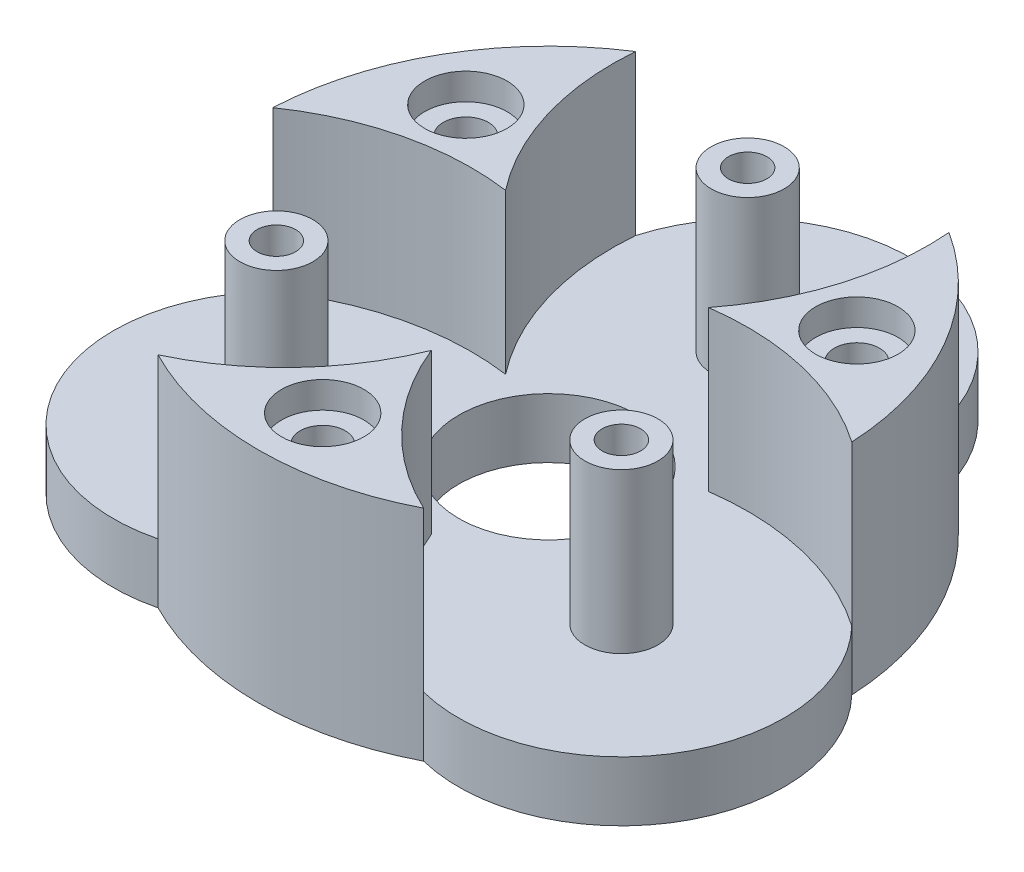
SolidWorks part; units mm, degrees
material "ABS"
ref_plane "Alzado" through (0, 0, 0) normal (0, 0, 1) x (1, 0, 0)
ref_plane "Planta" through (0, 0, 0) normal (0, 1, 0) x (1, 0, 0)
ref_plane "Vista lateral" through (0, 0, 0) normal (1, 0, 0) x (0, 0, -1)
sketch "Croquis1" plane through (0, 0, 0) normal (0, 1, 0) x (1, 0, 0)
  circle A0 centre (0, 0) radius 5 construction
  circle A1 centre (0, 15) radius 10 construction
  circle A2 centre (0, 0) radius 25 construction
  circle A7 centre (0, 0) radius 21.825
  point P24 (0, 0)
  dimension "D1" = 10
  dimension "D2" = 20
  dimension "D3" = 43.65
extrude "Saliente-Extruir1" add sketch "Croquis1" along normal blind 4.5
sketch "Croquis2" plane through (0, 4.5, 0) normal (0, 1, 0) x (1, 0, 0)
  circle A0 centre (0, 0) radius 15 construction
  circle A1 centre (0, 15) radius 2.75
  circle A2 centre (12.9904, -7.5) radius 2.75
  circle A3 centre (-12.9904, -7.5) radius 2.75
  point P12 (0, 0)
  dimension "D1" = 30
  dimension "D2" = 5.5
  dimension "D3" = 3
extrude "Saliente-Extruir2" add sketch "Croquis2" along normal blind 12
hole_wizard "Taladro de margen para M121" positions "Croquis3" profile "Croquis4" hole size "M12" standard "ISO" end condition through all
sketch "Croquis3" plane through (0, 4.5, 0) normal (0, 1, 0) x (1, 0, 0)
  point P0 (0, 0)
sketch "Croquis4" plane through (0, 4.5, 0) normal (1, 0, 0) x (0, 0, 1)
  line L0 (0, 0) -> (0, 4.5)
  line L1 (0, 4.5) -> (6.75, 4.5)
  line L2 (6.75, 4.5) -> (6.75, 0)
  line L5 (6.75, 0) -> (0, 0)
  line L11 (0, -6.35) -> (0, 107.95) construction
  dimension "Diámetro de taladro hasta el siguiente" = 13.5
  dimension "Profundidad de taladro hasta el siguiente" = 4.5
sketch "Croquis5" plane through (0, 4.5, 0) normal (0, 1, 0) x (1, 0, 0)
  line L0 (0, 0) -> (-18.901, 10.9125) construction
  line L1 (-12.9904, -7.5) -> (0, 15) construction
  circle A0 centre (-12.9904, -7.5) radius 8.25 construction
  circle A1 centre (0, 15) radius 8.25 construction
  arc A4 (-7.6427, 4.4125) -> (-11.8002, 18.3599) centre (8.1271, 16.7067) cw
  arc A5 (-7.6427, 4.4125) -> (-21.8002, 1.0394) centre (-10.4048, -15.3916) ccw
  arc A6 (-11.8002, 18.3599) -> (-21.8002, 1.0394) centre (0, 0) ccw
  circle A7 centre (0, 0) radius 21.825 construction
  dimension "D1" = 20
  dimension "D2" = 13
extrude "Saliente-Extruir3" add sketch "Croquis5" along normal up to surface (12 mm away) up to face at (-12.9904, 16.5, 10.25)
sketch "Croquis8" plane through (0, 16.5, 0) normal (0, 1, 0) x (1, 0, 0)
  line L0 (-7.6427, 4.4125) -> (-18.901, 10.9125) construction
  circle A1 centre (-14.7224, 8.5) radius 1.7
  circle A2 centre (0, 0) radius 15 construction
  arc A3 (-11.8002, 18.3599) -> (-21.8002, 1.0394) centre (0, 0) ccw construction
  circle A4 centre (0, 0) radius 17 construction
  dimension "D1" = 3.4
  dimension "D2" = 2
extrude "Cortar-Extruir1" cut sketch "Croquis8" against normal up to surface (16.5 mm away) up to face at (0, 0, 6.75)
pattern_circular "MatrizC1" count 3 over 360 about axis through (0, 0, 0) along (0, 1, 0) of "Saliente-Extruir3", "Cortar-Extruir1"
hole_wizard "Taladro de margen para M2.51" positions "Croquis9" profile "Croquis10" hole size "M2.5" standard "ISO" end condition through all
sketch "Croquis9" plane through (0, 16.5, 0) normal (0, 1, 0) x (1, 0, 0)
  point P0 (12.9904, -7.5)
  point P4 (-12.9904, -7.5)
  point P7 (0, 15)
sketch "Croquis10" plane through (12.9904, 16.5, 7.5) normal (1, 0, 0) x (0, 0, 1)
  line L0 (0, 0) -> (0, 16.5)
  line L1 (0, 16.5) -> (1.45, 16.5)
  line L2 (1.45, 16.5) -> (1.45, 0)
  line L5 (1.45, 0) -> (0, 0)
  line L11 (0, -6.35) -> (0, 107.95) construction
  dimension "Diámetro de taladro hasta el siguiente" = 2.9
  dimension "Profundidad de taladro hasta el siguiente" = 16.5
sketch "Croquis11" plane through (0, 0, 0) normal (0, -1, 0) x (1, 0, 0)
  arc A0 (-10, 19.3992) -> (-21.8002, -1.0394) centre (0, 0) ccw construction
  arc A1 (-10, 19.3992) -> (-21.8002, -1.0394) centre (0, 0) ccw
  arc A2 (-21.8002, -1.0394) -> (-10, 19.3992) centre (-12.9904, 7.5) cw
  circle A3 centre (-12.9904, 7.5) radius 1.45 construction
  circle A4 centre (-12.9904, 7.5) radius 1.45 construction
extrude "Saliente-Extruir5" add sketch "Croquis11" against normal up to surface (4.5 mm away) up to face at (0, 4.5, 6.75)
pattern_circular "MatrizC2" count 3 every 120 about axis through (0, 0, 0) along (0, 1, 0) of "Saliente-Extruir5"
sketch "Croquis12" plane through (0, 0, 0) normal (0, -1, 0) x (1, 0, 0)
  circle A0 centre (-12.9904, 7.5) radius 2.875
  circle A1 centre (12.9904, 7.5) radius 2.875
  circle A2 centre (0, -15) radius 2.875
  point P10 (0, 0)
  dimension "D1" = 5.75
  dimension "D2" = 3
extrude "Cortar-Extruir2" cut sketch "Croquis12" against normal blind 2.2
sketch "Croquis13" plane through (0, 16.5, 0) normal (0, 1, 0) x (1, 0, 0)
  circle A0 centre (0, -17) radius 3.1
  circle A2 centre (-14.7224, 8.5) radius 3.1
  circle A3 centre (14.7224, 8.5) radius 3.1
  point P11 (0, 0)
  dimension "D1" = 6.2
  dimension "D2" = 3
extrude "Cortar-Extruir3" cut sketch "Croquis13" against normal blind 2
sketch "Croquis14" plane through (0, 0, 0) normal (0, -1, 0) x (1, 0, 0)
  circle A0 centre (-14.7224, -8.5) radius 3.1
  dimension "D1" = 6.2
extrude "Cortar-Extruir4" cut sketch "Croquis14" against normal blind 3.5
